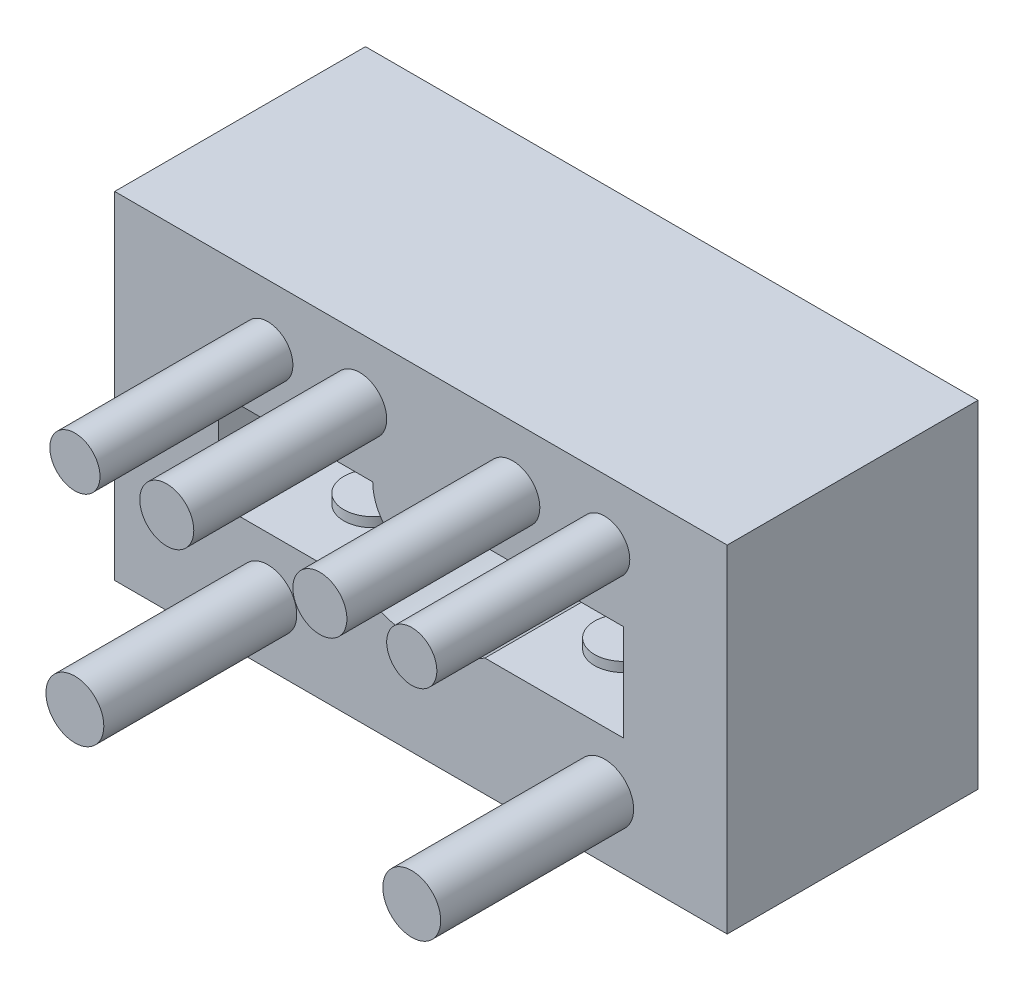
SolidWorks part; units mm, degrees
ref_plane "Front" through (0, 0, 0) normal (0, 0, 1) x (1, 0, 0)
ref_plane "Top" through (0, 0, 0) normal (0, 1, 0) x (1, 0, 0)
ref_plane "Right" through (0, 0, 0) normal (1, 0, 0) x (0, 0, -1)
sketch "Sketch1" plane through (0, 0, 0) normal (0, 0, 1) x (1, 0, 0)
  circle A0 centre (0, 0) radius 24
extrude "Extrude1" add sketch "Sketch1" along normal blind 5
sketch "Sketch2" plane through (0, 0, 5) normal (0, 0, 1) x (1, 0, 0)
  line L0 (-2.5, 0) -> (-10.5, 0)
  line L1 (2.5, 0) -> (10.5, 0)
  line L2 (10.5, 0) -> (10.5, -5)
  line L3 (10.5, -5) -> (-10.5, -5) construction
  line L4 (-10.5, -5) -> (-10.5, 0)
  line L5 (0, 0) -> (3.3166, -5) construction
  line L6 (0, 0) -> (-3.3166, -5) construction
  line L7 (-3.3166, -5) -> (-10.5, -5)
  line L8 (3.3166, -5) -> (10.5, -5)
  circle A0 centre (0, 0) radius 2.5 construction
  arc A1 (2.5, 0) -> (-2.5, 0) centre (0, 0) cw
  circle A2 centre (0, 0) radius 24
  circle A3 centre (0, 0) radius 6 construction
  arc A4 (3.3166, -5) -> (-3.3166, -5) centre (0, 0) cw
extrude "Extrude2" add sketch "Sketch2" along normal blind 8
sketch "Sketch7" plane through (0, 0, 0) normal (0, -1, 0) x (1, 0, 0)
  line L0 (10.5, 5) -> (2.5, 13) construction
  line L1 (24, 13) -> (-24, 13) construction
  line L2 (2.5, 13) -> (2.5, 5) construction
  line L3 (10.5, 13) -> (2.5, 5) construction
  line L4 (-10.5, 13) -> (-2.5, 5) construction
  line L5 (-2.5, 13) -> (-2.5, 5) construction
  line L7 (-2.5, 13) -> (-10.5, 5) construction
  circle A0 centre (-6.5, 9) radius 1.7
  circle A1 centre (6.5, 9) radius 1.7
  point P11 (6.5, 9)
  point P23 (-6.5, 9)
  dimension "D1" = 21
  dimension "D2" = 8
sketch "Sketch9" plane through (0, 0, 13) normal (0, 0, 1) x (1, 0, 0)
  line L0 (-15.875, 6.35) -> (15.875, 6.35)
  line L1 (15.875, 6.35) -> (15.875, -11.1125)
  line L2 (15.875, -11.1125) -> (-15.875, -11.1125)
  line L3 (-15.875, -11.1125) -> (-15.875, 6.35)
  circle A0 centre (0, 0) radius 24
extrude "Extrude4" cut sketch "Sketch9" against normal up to surface (13 mm away) up to face at (24, 0, 0)
sketch "Sketch10" plane through (0, 0, 13) normal (0, 0, 1) x (1, 0, 0)
  circle A0 centre (9.525, 3.175) radius 1.3
  circle A1 centre (-7.9375, 3.175) radius 1.3
  circle A2 centre (-7.9375, -7.9375) radius 1.5
  circle A3 centre (9.525, -7.9375) radius 1.5
  circle A4 centre (-3.175, 3.175) radius 1.4
  circle A5 centre (4.7625, 3.175) radius 1.4
extrude "Extrude5" add sketch "Sketch10" along normal blind 10
sketch "Sketch11" plane through (0, -5, 0) normal (0, 1, 0) x (1, 0, 0)
  line L0 (-2.5, -13) -> (-10.5, -5) construction
  circle A0 centre (-6.5, -9) radius 1.5
  circle A1 centre (6.5, -9) radius 1.5
  point P0 (-10.2731, -5.2269)
  point P1 (-2.5, -13)
  point P4 (-2.5, -5)
  point P6 (-10.5, -13)
  point P8 (2.5, -5)
  point P10 (10.5, -13)
  point P12 (10.5, -5)
  point P14 (2.5, -13)
  point P16 (-6.5, -9)
  point P18 (6.5, -9)
extrude "Extrude6" add sketch "Sketch11" along normal blind 0.5
